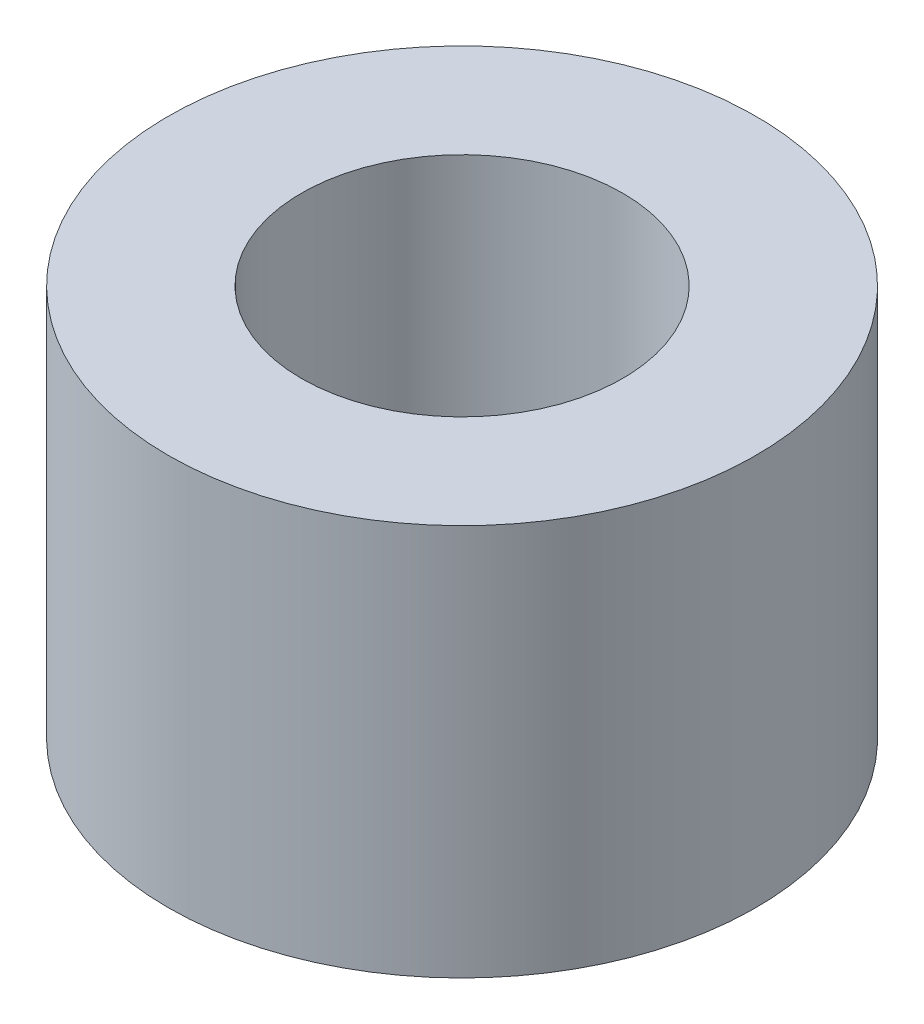
SolidWorks part; units mm, degrees
ref_plane "Front Plane" through (0, 0, 0) normal (0, 0, 1) x (1, 0, 0)
ref_plane "Top Plane" through (0, 0, 0) normal (0, 1, 0) x (1, 0, 0)
ref_plane "Right Plane" through (0, 0, 0) normal (1, 0, 0) x (0, 0, -1)
sketch "Sketch1" plane through (0, 0, 0) normal (0, 1, 0) x (1, 0, 0)
  circle A0 centre (0, 0) radius 2.05
  circle A1 centre (0, 0) radius 3.75
  dimension "D1" = 4.1
  dimension "D2" = 7.5
extrude "Boss-Extrude1" add sketch "Sketch1" along normal blind 5
